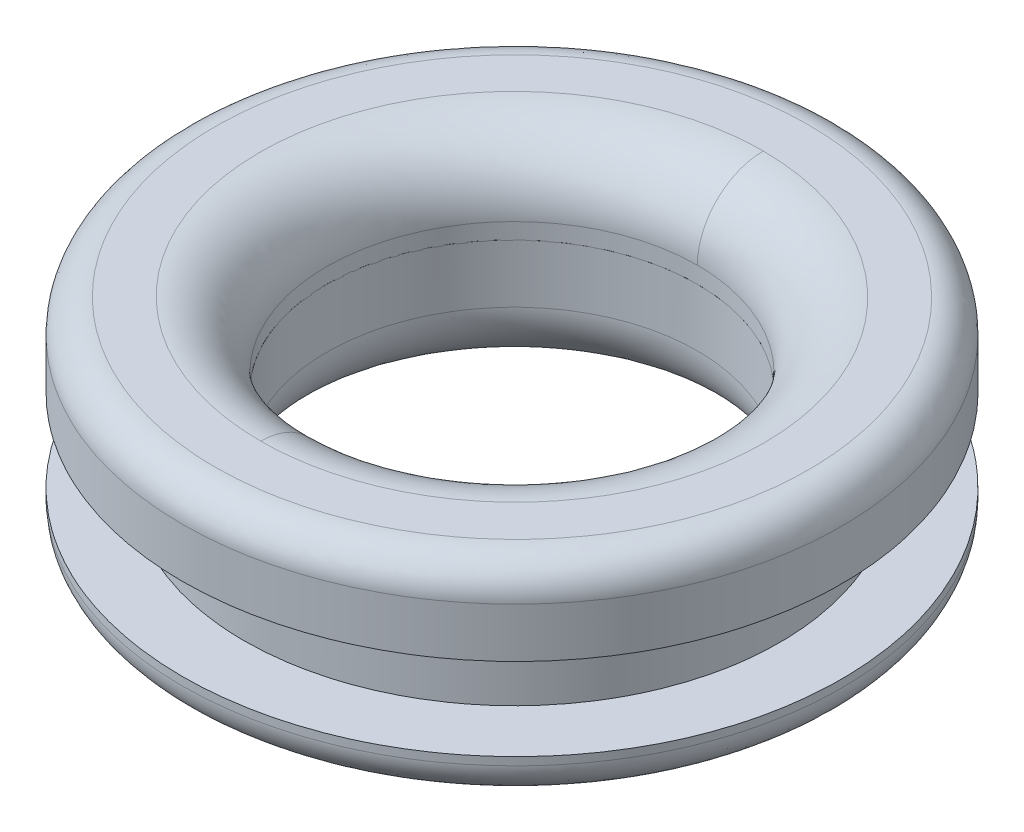
SolidWorks part; units mm, degrees
ref_plane "Plan de face" through (0, 0, 0) normal (0, 0, 1) x (1, 0, 0)
ref_plane "Plan de dessus" through (0, 0, 0) normal (0, 1, 0) x (1, 0, 0)
ref_plane "Plan de droite" through (0, 0, 0) normal (1, 0, 0) x (0, 0, -1)
sketch "Esquisse1" plane through (0, 0, 0) normal (0, 0, 1) x (1, 0, 0)
  line L0 (0, 0) -> (0, 11.2551) construction
  line L3 (4, -1.0267) -> (4, -1.5267)
  line L5 (-4, -1.0267) -> (-4, -1.5267)
  line L7 (-4, 0.9735) -> (-4, -0.0266)
  line L9 (4, 0.9735) -> (4, -0.0266)
  arc A0 (4, -1.0267) -> (-4, -1.0267) centre (0, -301) ccw
  arc A1 (4, -1.5267) -> (-4, -1.5267) centre (0, -301) ccw
  arc A2 (4, -0.0266) -> (-4, -0.0266) centre (0, -301) ccw
  arc A3 (4, 0.9735) -> (-4, 0.9735) centre (0, -301) ccw
  dimension "D4" = 300
  dimension "D5" = 301
  dimension "D2" = 302
  dimension "D3" = 299.5
  dimension "D1" = 8
extrude "Extrusion1" add sketch "Esquisse1" along normal mid plane 8
sketch "Esquisse2" plane through (0, 0, 0) normal (0, 1, 0) x (1, 0, 0)
  line L0 (4, -4) -> (4, 4) construction
  circle A0 centre (0, 0) radius 4
extrude "Enlèv. mat.-Extru.1" cut sketch "Esquisse2" against normal through all and the other way through all flip side to cut
sketch "Esquisse3" plane through (0, 0, 0) normal (0, 1, 0) x (1, 0, 0)
  circle A0 centre (0, 0) radius 3.25
  dimension "D1" = 6.5
extrude "Extrusion2" add sketch "Esquisse3" against normal up to surface (1 mm away)
sketch "Esquisse4" plane through (0, 0, 0) normal (0, 1, 0) x (1, 0, 0)
  circle A0 centre (0, 0) radius 2.25
  dimension "D1" = 4.5
extrude "Enlèv. mat.-Extru.2" cut sketch "Esquisse4" against normal through all and the other way through all
fillet "Congé1" radius 0.4 1 edges at (-0.9197, -1.5014, -3.8928)
fillet "Congé3" radius 0.4 1 edges at (0.9197, 0.9986, -3.8928)
fillet "Congé5" radius 0.8 2 edges
fillet "Congé6" radius 0.8 1 edges at (-0.5175, -1.5004, -2.1897)
